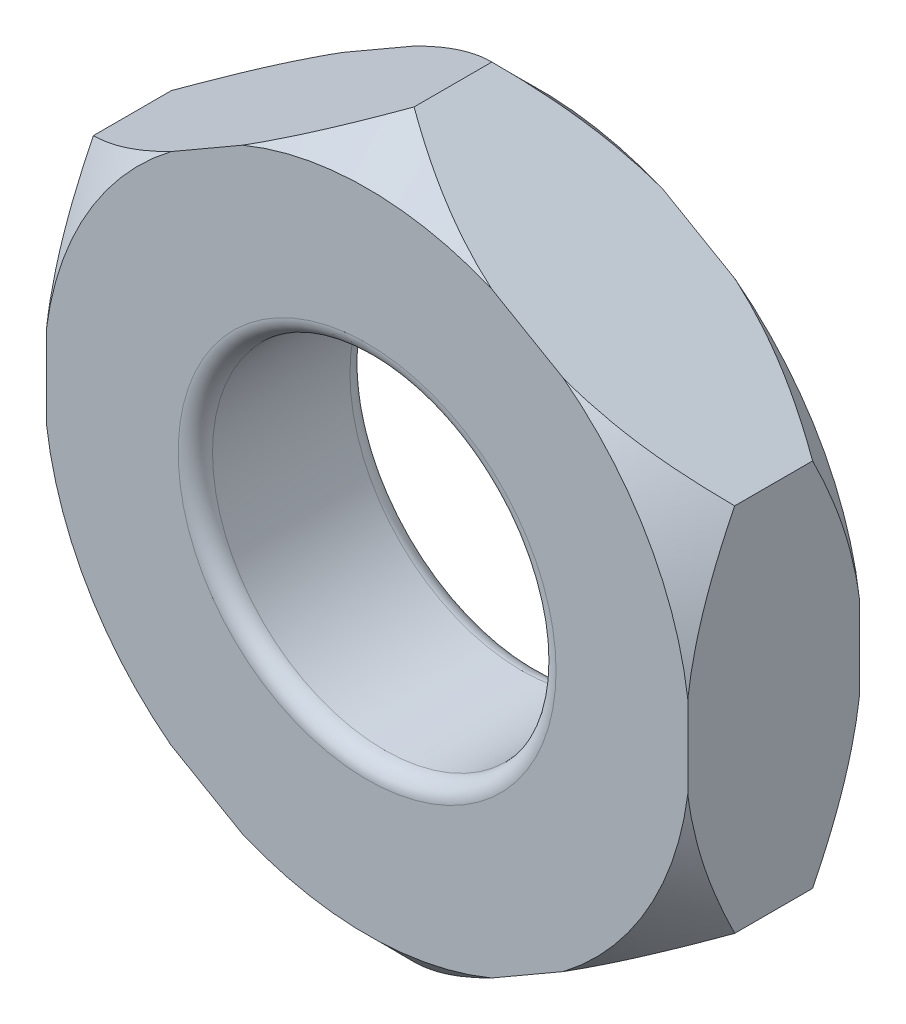
SolidWorks part; units mm, degrees
ref_plane "前视基准面" through (0, 0, 0) normal (0, 0, 1) x (1, 0, 0)
ref_plane "上视基准面" through (0, 0, 0) normal (0, 1, 0) x (1, 0, 0)
ref_plane "右视基准面" through (0, 0, 0) normal (1, 0, 0) x (0, 0, -1)
sketch "草图1" plane through (0, 0, 0) normal (0, 0, 1) x (1, 0, 0)
  line L1 (0, 3.2332) -> (-2.8, 1.6166)
  line L2 (-2.8, 1.6166) -> (-2.8, -1.6166)
  line L3 (-2.8, -1.6166) -> (0, -3.2332)
  line L4 (0, -3.2332) -> (2.8, -1.6166)
  line L5 (2.8, -1.6166) -> (2.8, 1.6166)
  line L6 (2.8, 1.6166) -> (0, 3.2332)
  circle A0 centre (0, 0) radius 2.8 construction
  dimension "D1" = 5.6
extrude "凸台-拉伸2" add sketch "草图1" against normal blind 1.5
sketch "草图2" plane through (0, 0, 0) normal (0, 0, 1) x (1, 0, 0)
  circle A0 centre (0, 0) radius 1.5
extrude "切除-拉伸1" cut sketch "草图2" against normal blind 1.5
fillet "圆角3" radius 0.15 2 edges at (1.5, 0, 0) (1.5, 0, -1.5)
sketch "草图3" plane through (0, 0, 0) normal (1, 0, 0) x (0, 0, -1)
  line L0 (0, 0) -> (2.7425, 0) construction
  line L1 (0, -1.6166) -> (0, 1.6166) construction
  line L2 (0, 3.2332) -> (0.41, 3.2332)
  line L3 (1.5, 3.2332) -> (0, 3.2332) construction
  line L4 (0.41, 3.2332) -> (0, 2.8232)
  line L5 (0, 1.6166) -> (0, 3.2332) construction
  line L6 (0, 2.8232) -> (0, 3.2332)
  line L7 (1.5, 3.2332) -> (1.09, 3.2332)
  line L8 (1.09, 3.2332) -> (1.5, 2.8232)
  line L9 (1.5, 1.6166) -> (1.5, 3.2332) construction
  line L10 (1.5, 2.8232) -> (1.5, 3.2332)
  point P15 (0, 0)
revolve "切除-旋转1" cut sketch "草图3" angle 360 about L0
